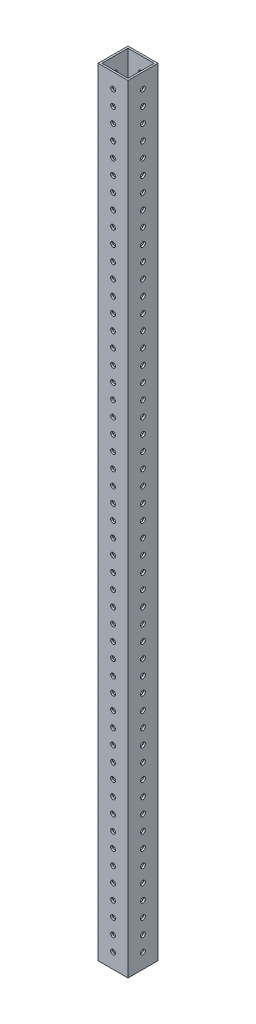
SolidWorks part; units mm, degrees
material "6061 Alloy"
ref_plane "Front Plane" through (0, 0, 0) normal (0, 0, 1) x (1, 0, 0)
ref_plane "Top Plane" through (0, 0, 0) normal (0, 1, 0) x (1, 0, 0)
ref_plane "Right Plane" through (0, 0, 0) normal (1, 0, 0) x (0, 0, -1)
sketch "Sketch1" plane through (0, 0, 0) normal (0, 1, 0) x (1, 0, 0)
  line L0 (1.5875, 1.5875) -> (1.5875, 23.8125)
  line L1 (0, 0) -> (25.4, 0)
  line L2 (0, 0) -> (0, 25.4)
  line L3 (0, 25.4) -> (25.4, 25.4)
  line L4 (25.4, 0) -> (25.4, 25.4)
  line L5 (1.5875, 23.8125) -> (23.8125, 23.8125)
  line L6 (23.8125, 1.5875) -> (23.8125, 23.8125)
  line L7 (1.5875, 1.5875) -> (23.8125, 1.5875)
  dimension "D2" = 25.4
  dimension "D3" = 25.4
  dimension "D1" = 1.5875
extrude "Boss-Extrude1" add sketch "Sketch1" along normal blind 660.4
sketch "Sketch2" plane through (0, 0, 0) normal (0, 0, 1) x (1, 0, 0)
  line L0 (0, 0) -> (25.4, 0) construction
  line L1 (0, 660.4) -> (0, 0) construction
  circle A0 centre (12.7, 12.7) radius 2.0193
  circle A1 centre (12.7, 25.4) radius 2.0193
  circle A2 centre (12.7, 38.1) radius 2.0193
  circle A3 centre (12.7, 50.8) radius 2.0193
  circle A4 centre (12.7, 63.5) radius 2.0193
  circle A5 centre (12.7, 76.2) radius 2.0193
  circle A6 centre (12.7, 88.9) radius 2.0193
  circle A7 centre (12.7, 101.6) radius 2.0193
  circle A8 centre (12.7, 114.3) radius 2.0193
  circle A9 centre (12.7, 127) radius 2.0193
  circle A10 centre (12.7, 139.7) radius 2.0193
  circle A11 centre (12.7, 152.4) radius 2.0193
  circle A12 centre (12.7, 165.1) radius 2.0193
  circle A13 centre (12.7, 177.8) radius 2.0193
  circle A14 centre (12.7, 190.5) radius 2.0193
  circle A15 centre (12.7, 203.2) radius 2.0193
  circle A16 centre (12.7, 215.9) radius 2.0193
  circle A17 centre (12.7, 228.6) radius 2.0193
  circle A18 centre (12.7, 241.3) radius 2.0193
  circle A19 centre (12.7, 254) radius 2.0193
  circle A20 centre (12.7, 266.7) radius 2.0193
  circle A21 centre (12.7, 279.4) radius 2.0193
  circle A22 centre (12.7, 292.1) radius 2.0193
  circle A23 centre (12.7, 304.8) radius 2.0193
  circle A24 centre (12.7, 317.5) radius 2.0193
  circle A25 centre (12.7, 330.2) radius 2.0193
  circle A26 centre (12.7, 342.9) radius 2.0193
  circle A27 centre (12.7, 355.6) radius 2.0193
  circle A28 centre (12.7, 368.3) radius 2.0193
  circle A29 centre (12.7, 381) radius 2.0193
  circle A30 centre (12.7, 393.7) radius 2.0193
  circle A31 centre (12.7, 406.4) radius 2.0193
  circle A32 centre (12.7, 419.1) radius 2.0193
  circle A33 centre (12.7, 431.8) radius 2.0193
  circle A34 centre (12.7, 444.5) radius 2.0193
  circle A35 centre (12.7, 457.2) radius 2.0193
  circle A36 centre (12.7, 469.9) radius 2.0193
  circle A37 centre (12.7, 482.6) radius 2.0193
  circle A38 centre (12.7, 495.3) radius 2.0193
  circle A39 centre (12.7, 508) radius 2.0193
  circle A40 centre (12.7, 520.7) radius 2.0193
  circle A41 centre (12.7, 533.4) radius 2.0193
  circle A42 centre (12.7, 546.1) radius 2.0193
  circle A43 centre (12.7, 558.8) radius 2.0193
  circle A44 centre (12.7, 571.5) radius 2.0193
  circle A45 centre (12.7, 584.2) radius 2.0193
  circle A46 centre (12.7, 596.9) radius 2.0193
  circle A47 centre (12.7, 609.6) radius 2.0193
  circle A48 centre (12.7, 622.3) radius 2.0193
  circle A49 centre (12.7, 635) radius 2.0193
  circle A50 centre (12.7, 647.7) radius 2.0193
  dimension "D3" = 4.0386
  dimension "D1" = 12.7
  dimension "D2" = 12.7
  dimension "D5" = 12.7
  dimension "D4" = 51
extrude "Cut-Extrude1" cut sketch "Sketch2" against normal through all
sketch "Sketch3" plane through (25.4, 0, 0) normal (1, 0, 0) x (0, 0, -1)
  line L2 (25.4, 660.4) -> (25.4, 0) construction
  line L3 (0, 0) -> (25.4, 0) construction
  circle A0 centre (12.7, 12.7) radius 2.0193
  circle A1 centre (12.7, 25.4) radius 2.0193
  circle A2 centre (12.7, 38.1) radius 2.0193
  circle A3 centre (12.7, 50.8) radius 2.0193
  circle A4 centre (12.7, 63.5) radius 2.0193
  circle A5 centre (12.7, 76.2) radius 2.0193
  circle A6 centre (12.7, 88.9) radius 2.0193
  circle A7 centre (12.7, 101.6) radius 2.0193
  circle A8 centre (12.7, 114.3) radius 2.0193
  circle A9 centre (12.7, 127) radius 2.0193
  circle A10 centre (12.7, 139.7) radius 2.0193
  circle A11 centre (12.7, 152.4) radius 2.0193
  circle A12 centre (12.7, 165.1) radius 2.0193
  circle A13 centre (12.7, 177.8) radius 2.0193
  circle A14 centre (12.7, 190.5) radius 2.0193
  circle A15 centre (12.7, 203.2) radius 2.0193
  circle A16 centre (12.7, 215.9) radius 2.0193
  circle A17 centre (12.7, 228.6) radius 2.0193
  circle A18 centre (12.7, 241.3) radius 2.0193
  circle A19 centre (12.7, 254) radius 2.0193
  circle A20 centre (12.7, 266.7) radius 2.0193
  circle A21 centre (12.7, 279.4) radius 2.0193
  circle A22 centre (12.7, 292.1) radius 2.0193
  circle A23 centre (12.7, 304.8) radius 2.0193
  circle A24 centre (12.7, 317.5) radius 2.0193
  circle A25 centre (12.7, 330.2) radius 2.0193
  circle A26 centre (12.7, 342.9) radius 2.0193
  circle A27 centre (12.7, 355.6) radius 2.0193
  circle A28 centre (12.7, 368.3) radius 2.0193
  circle A29 centre (12.7, 381) radius 2.0193
  circle A30 centre (12.7, 393.7) radius 2.0193
  circle A31 centre (12.7, 406.4) radius 2.0193
  circle A32 centre (12.7, 419.1) radius 2.0193
  circle A33 centre (12.7, 431.8) radius 2.0193
  circle A34 centre (12.7, 444.5) radius 2.0193
  circle A35 centre (12.7, 457.2) radius 2.0193
  circle A36 centre (12.7, 469.9) radius 2.0193
  circle A37 centre (12.7, 482.6) radius 2.0193
  circle A38 centre (12.7, 495.3) radius 2.0193
  circle A39 centre (12.7, 508) radius 2.0193
  circle A40 centre (12.7, 520.7) radius 2.0193
  circle A41 centre (12.7, 533.4) radius 2.0193
  circle A42 centre (12.7, 546.1) radius 2.0193
  circle A43 centre (12.7, 558.8) radius 2.0193
  circle A44 centre (12.7, 571.5) radius 2.0193
  circle A45 centre (12.7, 584.2) radius 2.0193
  circle A46 centre (12.7, 596.9) radius 2.0193
  circle A47 centre (12.7, 609.6) radius 2.0193
  circle A48 centre (12.7, 622.3) radius 2.0193
  circle A49 centre (12.7, 635) radius 2.0193
  circle A50 centre (12.7, 647.7) radius 2.0193
  dimension "D3" = 4.0386
  dimension "D1" = 12.7
  dimension "D2" = 12.7
  dimension "D5" = 12.7
  dimension "D4" = 51
extrude "Cut-Extrude2" cut sketch "Sketch3" against normal through all
equation "\"Bar thickness\" = 0.0625"
equation "\"Length\" = 26"
equation "\"D1@Sketch1\"=\"Bar thickness\""
equation "\"D1@Boss-Extrude1\"=\"Length\""
equation "\"D4@Sketch2\"= \"Length\" * 2 -1"
equation "\"D4@Sketch3\"= \"Length\" * 2 -1"
